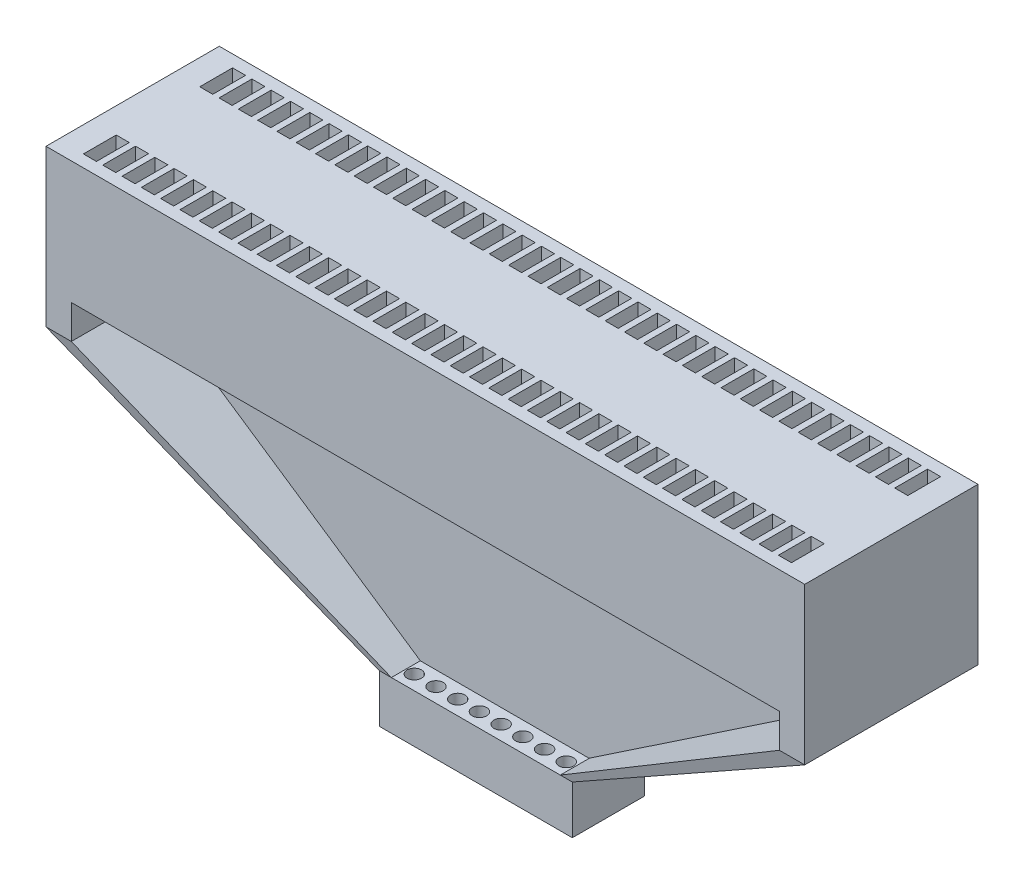
SolidWorks part; units mm, degrees
ref_plane "Front Plane" through (0, 0, 0) normal (0, 0, 1) x (1, 0, 0)
ref_plane "Top Plane" through (0, 0, 0) normal (0, 1, 0) x (1, 0, 0)
ref_plane "Right Plane" through (0, 0, 0) normal (1, 0, 0) x (0, 0, -1)
sketch "main block" plane through (0, 0, 0) normal (0, 1, 0) x (1, 0, 0)
  line L1 (7.86, -1.795) -> (-7.86, -1.795)
  line L2 (7.86, -1.795) -> (7.86, 1.795)
  line L3 (7.86, 1.795) -> (-7.86, 1.795)
  line L4 (-7.86, -1.795) -> (-7.86, 1.795)
  line L5 (7.86, -1.795) -> (-7.86, 1.795) construction
  line L6 (7.86, 1.795) -> (-7.86, -1.795) construction
  point P0 (0, 0)
  dimension "D1" = 15.72
  dimension "D2" = 3.59
extrude "Main Well Block" add sketch "main block" against normal blind 2.54
sketch "well sketch" plane through (0, 0, 0) normal (0, 1, 0) x (1, 0, 0)
  line L0 (7.86, -1.795) -> (7.86, 1.795) construction
  line L1 (7.3349, 1.545) -> (7.0649, 1.545)
  line L2 (7.3349, 1.545) -> (7.3349, 0.865)
  line L3 (7.3349, 0.865) -> (7.0649, 0.865)
  line L4 (7.0649, 1.545) -> (7.0649, 0.865)
  line L5 (7.86, 1.795) -> (-7.86, 1.795) construction
  line L6 (6.9349, 1.545) -> (6.6649, 1.545)
  line L7 (6.9349, 1.545) -> (6.9349, 0.865)
  line L8 (6.9349, 0.865) -> (6.6649, 0.865)
  line L9 (6.6649, 1.545) -> (6.6649, 0.865)
  line L10 (6.5349, 1.545) -> (6.2649, 1.545)
  line L11 (6.5349, 1.545) -> (6.5349, 0.865)
  line L12 (6.5349, 0.865) -> (6.2649, 0.865)
  line L13 (6.2649, 1.545) -> (6.2649, 0.865)
  line L14 (6.1349, 1.545) -> (5.8649, 1.545)
  line L15 (6.1349, 1.545) -> (6.1349, 0.865)
  line L16 (6.1349, 0.865) -> (5.8649, 0.865)
  line L17 (5.8649, 1.545) -> (5.8649, 0.865)
  line L18 (5.7349, 1.545) -> (5.4649, 1.545)
  line L19 (5.7349, 1.545) -> (5.7349, 0.865)
  line L20 (5.7349, 0.865) -> (5.4649, 0.865)
  line L21 (5.4649, 1.545) -> (5.4649, 0.865)
  line L22 (5.3349, 1.545) -> (5.0649, 1.545)
  line L23 (5.3349, 1.545) -> (5.3349, 0.865)
  line L24 (5.3349, 0.865) -> (5.0649, 0.865)
  line L25 (5.0649, 1.545) -> (5.0649, 0.865)
  line L26 (4.9349, 1.545) -> (4.6649, 1.545)
  line L27 (4.9349, 1.545) -> (4.9349, 0.865)
  line L28 (4.9349, 0.865) -> (4.6649, 0.865)
  line L29 (4.6649, 1.545) -> (4.6649, 0.865)
  line L30 (4.5349, 1.545) -> (4.2649, 1.545)
  line L31 (4.5349, 1.545) -> (4.5349, 0.865)
  line L32 (4.5349, 0.865) -> (4.2649, 0.865)
  line L33 (4.2649, 1.545) -> (4.2649, 0.865)
  line L34 (4.135, 1.545) -> (3.865, 1.545)
  line L35 (4.135, 1.545) -> (4.135, 0.865)
  line L36 (4.135, 0.865) -> (3.865, 0.865)
  line L37 (3.865, 1.545) -> (3.865, 0.865)
  line L38 (3.735, 1.545) -> (3.465, 1.545)
  line L39 (3.735, 1.545) -> (3.735, 0.865)
  line L40 (3.735, 0.865) -> (3.465, 0.865)
  line L41 (3.465, 1.545) -> (3.465, 0.865)
  line L42 (3.335, 1.545) -> (3.065, 1.545)
  line L43 (3.335, 1.545) -> (3.335, 0.865)
  line L44 (3.335, 0.865) -> (3.065, 0.865)
  line L45 (3.065, 1.545) -> (3.065, 0.865)
  line L46 (2.935, 1.545) -> (2.665, 1.545)
  line L47 (2.935, 1.545) -> (2.935, 0.865)
  line L48 (2.935, 0.865) -> (2.665, 0.865)
  line L49 (2.665, 1.545) -> (2.665, 0.865)
  line L50 (2.535, 1.545) -> (2.265, 1.545)
  line L51 (2.535, 1.545) -> (2.535, 0.865)
  line L52 (2.535, 0.865) -> (2.265, 0.865)
  line L53 (2.265, 1.545) -> (2.265, 0.865)
  line L54 (2.135, 1.545) -> (1.865, 1.545)
  line L55 (2.135, 1.545) -> (2.135, 0.865)
  line L56 (2.135, 0.865) -> (1.865, 0.865)
  line L57 (1.865, 1.545) -> (1.865, 0.865)
  line L58 (1.735, 1.545) -> (1.465, 1.545)
  line L59 (1.735, 1.545) -> (1.735, 0.865)
  line L60 (1.735, 0.865) -> (1.465, 0.865)
  line L61 (1.465, 1.545) -> (1.465, 0.865)
  line L62 (1.335, 1.545) -> (1.065, 1.545)
  line L63 (1.335, 1.545) -> (1.335, 0.865)
  line L64 (1.335, 0.865) -> (1.065, 0.865)
  line L65 (1.065, 1.545) -> (1.065, 0.865)
  line L66 (0.935, 1.545) -> (0.665, 1.545)
  line L67 (0.935, 1.545) -> (0.935, 0.865)
  line L68 (0.935, 0.865) -> (0.665, 0.865)
  line L69 (0.665, 1.545) -> (0.665, 0.865)
  line L70 (0.535, 1.545) -> (0.265, 1.545)
  line L71 (0.535, 1.545) -> (0.535, 0.865)
  line L72 (0.535, 0.865) -> (0.265, 0.865)
  line L73 (0.265, 1.545) -> (0.265, 0.865)
  line L74 (0.135, 1.545) -> (-0.135, 1.545)
  line L75 (0.135, 1.545) -> (0.135, 0.865)
  line L76 (0.135, 0.865) -> (-0.135, 0.865)
  line L77 (-0.135, 1.545) -> (-0.135, 0.865)
  line L78 (-0.265, 1.545) -> (-0.535, 1.545)
  line L79 (-0.265, 1.545) -> (-0.265, 0.865)
  line L80 (-0.265, 0.865) -> (-0.535, 0.865)
  line L81 (-0.535, 1.545) -> (-0.535, 0.865)
  line L82 (-0.665, 1.545) -> (-0.935, 1.545)
  line L83 (-0.665, 1.545) -> (-0.665, 0.865)
  line L84 (-0.665, 0.865) -> (-0.935, 0.865)
  line L85 (-0.935, 1.545) -> (-0.935, 0.865)
  line L86 (-1.065, 1.545) -> (-1.335, 1.545)
  line L87 (-1.065, 1.545) -> (-1.065, 0.865)
  line L88 (-1.065, 0.865) -> (-1.335, 0.865)
  line L89 (-1.335, 1.545) -> (-1.335, 0.865)
  line L90 (-1.465, 1.545) -> (-1.735, 1.545)
  line L91 (-1.465, 1.545) -> (-1.465, 0.865)
  line L92 (-1.465, 0.865) -> (-1.735, 0.865)
  line L93 (-1.735, 1.545) -> (-1.735, 0.865)
  line L94 (-1.8649, 1.545) -> (-2.1349, 1.545)
  line L95 (-1.8649, 1.545) -> (-1.8649, 0.865)
  line L96 (-1.8649, 0.865) -> (-2.1349, 0.865)
  line L97 (-2.1349, 1.545) -> (-2.1349, 0.865)
  line L98 (-2.2649, 1.545) -> (-2.5349, 1.545)
  line L99 (-2.2649, 1.545) -> (-2.2649, 0.865)
  line L100 (-2.2649, 0.865) -> (-2.5349, 0.865)
  line L101 (-2.5349, 1.545) -> (-2.5349, 0.865)
  line L102 (-2.6649, 1.545) -> (-2.9349, 1.545)
  line L103 (-2.6649, 1.545) -> (-2.6649, 0.865)
  line L104 (-2.6649, 0.865) -> (-2.9349, 0.865)
  line L105 (-2.9349, 1.545) -> (-2.9349, 0.865)
  line L106 (-3.0649, 1.545) -> (-3.3349, 1.545)
  line L107 (-3.0649, 1.545) -> (-3.0649, 0.865)
  line L108 (-3.0649, 0.865) -> (-3.3349, 0.865)
  line L109 (-3.3349, 1.545) -> (-3.3349, 0.865)
  line L110 (-3.4649, 1.545) -> (-3.7349, 1.545)
  line L111 (-3.4649, 1.545) -> (-3.4649, 0.865)
  line L112 (-3.4649, 0.865) -> (-3.7349, 0.865)
  line L113 (-3.7349, 1.545) -> (-3.7349, 0.865)
  line L114 (-3.8649, 1.545) -> (-4.1349, 1.545)
  line L115 (-3.8649, 1.545) -> (-3.8649, 0.865)
  line L116 (-3.8649, 0.865) -> (-4.1349, 0.865)
  line L117 (-4.1349, 1.545) -> (-4.1349, 0.865)
  line L118 (-4.2649, 1.545) -> (-4.5349, 1.545)
  line L119 (-4.2649, 1.545) -> (-4.2649, 0.865)
  line L120 (-4.2649, 0.865) -> (-4.5349, 0.865)
  line L121 (-4.5349, 1.545) -> (-4.5349, 0.865)
  line L122 (-4.6649, 1.545) -> (-4.9349, 1.545)
  line L123 (-4.6649, 1.545) -> (-4.6649, 0.865)
  line L124 (-4.6649, 0.865) -> (-4.9349, 0.865)
  line L125 (-4.9349, 1.545) -> (-4.9349, 0.865)
  line L126 (-5.0649, 1.545) -> (-5.3349, 1.545)
  line L127 (-5.0649, 1.545) -> (-5.0649, 0.865)
  line L128 (-5.0649, 0.865) -> (-5.3349, 0.865)
  line L129 (-5.3349, 1.545) -> (-5.3349, 0.865)
  line L130 (-5.4649, 1.545) -> (-5.7349, 1.545)
  line L131 (-5.4649, 1.545) -> (-5.4649, 0.865)
  line L132 (-5.4649, 0.865) -> (-5.7349, 0.865)
  line L133 (-5.7349, 1.545) -> (-5.7349, 0.865)
  line L134 (-5.8649, 1.545) -> (-6.1349, 1.545)
  line L135 (-5.8649, 1.545) -> (-5.8649, 0.865)
  line L136 (-5.8649, 0.865) -> (-6.1349, 0.865)
  line L137 (-6.1349, 1.545) -> (-6.1349, 0.865)
  line L138 (-6.2649, 1.545) -> (-6.5349, 1.545)
  line L139 (-6.2649, 1.545) -> (-6.2649, 0.865)
  line L140 (-6.2649, 0.865) -> (-6.5349, 0.865)
  line L141 (-6.5349, 1.545) -> (-6.5349, 0.865)
  line L142 (6.9349, -0.865) -> (6.6649, -0.865)
  line L143 (6.9349, -0.865) -> (6.9349, -1.545)
  line L144 (6.9349, -1.545) -> (6.6649, -1.545)
  line L145 (6.6649, -0.865) -> (6.6649, -1.545)
  line L146 (6.5349, -0.865) -> (6.2649, -0.865)
  line L147 (6.5349, -0.865) -> (6.5349, -1.545)
  line L148 (6.5349, -1.545) -> (6.2649, -1.545)
  line L149 (6.2649, -0.865) -> (6.2649, -1.545)
  line L150 (6.1349, -0.865) -> (5.8649, -0.865)
  line L151 (6.1349, -0.865) -> (6.1349, -1.545)
  line L152 (6.1349, -1.545) -> (5.8649, -1.545)
  line L153 (5.8649, -0.865) -> (5.8649, -1.545)
  line L154 (5.7349, -0.865) -> (5.4649, -0.865)
  line L155 (5.7349, -0.865) -> (5.7349, -1.545)
  line L156 (5.7349, -1.545) -> (5.4649, -1.545)
  line L157 (5.4649, -0.865) -> (5.4649, -1.545)
  line L158 (5.3349, -0.865) -> (5.0649, -0.865)
  line L159 (5.3349, -0.865) -> (5.3349, -1.545)
  line L160 (5.3349, -1.545) -> (5.0649, -1.545)
  line L161 (5.0649, -0.865) -> (5.0649, -1.545)
  line L162 (4.9349, -0.865) -> (4.6649, -0.865)
  line L163 (4.9349, -0.865) -> (4.9349, -1.545)
  line L164 (4.9349, -1.545) -> (4.6649, -1.545)
  line L165 (4.6649, -0.865) -> (4.6649, -1.545)
  line L166 (4.5349, -0.865) -> (4.2649, -0.865)
  line L167 (4.5349, -0.865) -> (4.5349, -1.545)
  line L168 (4.5349, -1.545) -> (4.2649, -1.545)
  line L169 (4.2649, -0.865) -> (4.2649, -1.545)
  line L170 (4.135, -0.865) -> (3.865, -0.865)
  line L171 (4.135, -0.865) -> (4.135, -1.545)
  line L172 (4.135, -1.545) -> (3.865, -1.545)
  line L173 (3.865, -0.865) -> (3.865, -1.545)
  line L174 (3.735, -0.865) -> (3.465, -0.865)
  line L175 (3.735, -0.865) -> (3.735, -1.545)
  line L176 (3.735, -1.545) -> (3.465, -1.545)
  line L177 (3.465, -0.865) -> (3.465, -1.545)
  line L178 (3.335, -0.865) -> (3.065, -0.865)
  line L179 (3.335, -0.865) -> (3.335, -1.545)
  line L180 (3.335, -1.545) -> (3.065, -1.545)
  line L181 (3.065, -0.865) -> (3.065, -1.545)
  line L182 (2.935, -0.865) -> (2.665, -0.865)
  line L183 (2.935, -0.865) -> (2.935, -1.545)
  line L184 (2.935, -1.545) -> (2.665, -1.545)
  line L185 (2.665, -0.865) -> (2.665, -1.545)
  line L186 (2.535, -0.865) -> (2.265, -0.865)
  line L187 (2.535, -0.865) -> (2.535, -1.545)
  line L188 (2.535, -1.545) -> (2.265, -1.545)
  line L189 (2.265, -0.865) -> (2.265, -1.545)
  line L190 (2.135, -0.865) -> (1.865, -0.865)
  line L191 (2.135, -0.865) -> (2.135, -1.545)
  line L192 (2.135, -1.545) -> (1.865, -1.545)
  line L193 (1.865, -0.865) -> (1.865, -1.545)
  line L194 (1.735, -0.865) -> (1.465, -0.865)
  line L195 (1.735, -0.865) -> (1.735, -1.545)
  line L196 (1.735, -1.545) -> (1.465, -1.545)
  line L197 (1.465, -0.865) -> (1.465, -1.545)
  line L198 (1.335, -0.865) -> (1.065, -0.865)
  line L199 (1.335, -0.865) -> (1.335, -1.545)
  line L200 (1.335, -1.545) -> (1.065, -1.545)
  line L201 (1.065, -0.865) -> (1.065, -1.545)
  line L202 (0.935, -0.865) -> (0.665, -0.865)
  line L203 (0.935, -0.865) -> (0.935, -1.545)
  line L204 (0.935, -1.545) -> (0.665, -1.545)
  line L205 (0.665, -0.865) -> (0.665, -1.545)
  line L206 (0.535, -0.865) -> (0.265, -0.865)
  line L207 (0.535, -0.865) -> (0.535, -1.545)
  line L208 (0.535, -1.545) -> (0.265, -1.545)
  line L209 (0.265, -0.865) -> (0.265, -1.545)
  line L210 (0.135, -0.865) -> (-0.135, -0.865)
  line L211 (0.135, -0.865) -> (0.135, -1.545)
  line L212 (0.135, -1.545) -> (-0.135, -1.545)
  line L213 (-0.135, -0.865) -> (-0.135, -1.545)
  line L214 (-0.265, -0.865) -> (-0.535, -0.865)
  line L215 (-0.265, -0.865) -> (-0.265, -1.545)
  line L216 (-0.265, -1.545) -> (-0.535, -1.545)
  line L217 (-0.535, -0.865) -> (-0.535, -1.545)
  line L218 (-0.665, -0.865) -> (-0.935, -0.865)
  line L219 (-0.665, -0.865) -> (-0.665, -1.545)
  line L220 (-0.665, -1.545) -> (-0.935, -1.545)
  line L221 (-0.935, -0.865) -> (-0.935, -1.545)
  line L222 (-1.065, -0.865) -> (-1.335, -0.865)
  line L223 (-1.065, -0.865) -> (-1.065, -1.545)
  line L224 (-1.065, -1.545) -> (-1.335, -1.545)
  line L225 (-1.335, -0.865) -> (-1.335, -1.545)
  line L226 (-1.465, -0.865) -> (-1.735, -0.865)
  line L227 (-1.465, -0.865) -> (-1.465, -1.545)
  line L228 (-1.465, -1.545) -> (-1.735, -1.545)
  line L229 (-1.735, -0.865) -> (-1.735, -1.545)
  line L230 (-1.8649, -0.865) -> (-2.1349, -0.865)
  line L231 (-1.8649, -0.865) -> (-1.8649, -1.545)
  line L232 (-1.8649, -1.545) -> (-2.1349, -1.545)
  line L233 (-2.1349, -0.865) -> (-2.1349, -1.545)
  line L234 (-2.2649, -0.865) -> (-2.5349, -0.865)
  line L235 (-2.2649, -0.865) -> (-2.2649, -1.545)
  line L236 (-2.2649, -1.545) -> (-2.5349, -1.545)
  line L237 (-2.5349, -0.865) -> (-2.5349, -1.545)
  line L238 (-2.6649, -0.865) -> (-2.9349, -0.865)
  line L239 (-2.6649, -0.865) -> (-2.6649, -1.545)
  line L240 (-2.6649, -1.545) -> (-2.9349, -1.545)
  line L241 (-2.9349, -0.865) -> (-2.9349, -1.545)
  line L242 (-3.0649, -0.865) -> (-3.3349, -0.865)
  line L243 (-3.0649, -0.865) -> (-3.0649, -1.545)
  line L244 (-3.0649, -1.545) -> (-3.3349, -1.545)
  line L245 (-3.3349, -0.865) -> (-3.3349, -1.545)
  line L246 (-3.4649, -0.865) -> (-3.7349, -0.865)
  line L247 (-3.4649, -0.865) -> (-3.4649, -1.545)
  line L248 (-3.4649, -1.545) -> (-3.7349, -1.545)
  line L249 (-3.7349, -0.865) -> (-3.7349, -1.545)
  line L250 (-3.8649, -0.865) -> (-4.1349, -0.865)
  line L251 (-3.8649, -0.865) -> (-3.8649, -1.545)
  line L252 (-3.8649, -1.545) -> (-4.1349, -1.545)
  line L253 (-4.1349, -0.865) -> (-4.1349, -1.545)
  line L254 (-4.2649, -0.865) -> (-4.5349, -0.865)
  line L255 (-4.2649, -0.865) -> (-4.2649, -1.545)
  line L256 (-4.2649, -1.545) -> (-4.5349, -1.545)
  line L257 (-4.5349, -0.865) -> (-4.5349, -1.545)
  line L258 (-4.6649, -0.865) -> (-4.9349, -0.865)
  line L259 (-4.6649, -0.865) -> (-4.6649, -1.545)
  line L260 (-4.6649, -1.545) -> (-4.9349, -1.545)
  line L261 (-4.9349, -0.865) -> (-4.9349, -1.545)
  line L262 (-5.0649, -0.865) -> (-5.3349, -0.865)
  line L263 (-5.0649, -0.865) -> (-5.0649, -1.545)
  line L264 (-5.0649, -1.545) -> (-5.3349, -1.545)
  line L265 (-5.3349, -0.865) -> (-5.3349, -1.545)
  line L266 (-5.4649, -0.865) -> (-5.7349, -0.865)
  line L267 (-5.4649, -0.865) -> (-5.4649, -1.545)
  line L268 (-5.4649, -1.545) -> (-5.7349, -1.545)
  line L269 (-5.7349, -0.865) -> (-5.7349, -1.545)
  line L270 (-5.8649, -0.865) -> (-6.1349, -0.865)
  line L271 (-5.8649, -0.865) -> (-5.8649, -1.545)
  line L272 (-5.8649, -1.545) -> (-6.1349, -1.545)
  line L273 (-6.1349, -0.865) -> (-6.1349, -1.545)
  line L274 (-6.2649, -0.865) -> (-6.5349, -0.865)
  line L275 (-6.2649, -0.865) -> (-6.2649, -1.545)
  line L276 (-6.2649, -1.545) -> (-6.5349, -1.545)
  line L277 (-6.5349, -0.865) -> (-6.5349, -1.545)
  line L278 (7.3349, -0.865) -> (7.0649, -0.865)
  line L279 (7.3349, -0.865) -> (7.3349, -1.545)
  line L280 (7.3349, -1.545) -> (7.0649, -1.545)
  line L281 (7.0649, -0.865) -> (7.0649, -1.545)
  line L282 (-6.6649, 1.545) -> (-6.9349, 1.545)
  line L283 (-6.6649, 1.545) -> (-6.6649, 0.865)
  line L284 (-6.6649, 0.865) -> (-6.9349, 0.865)
  line L285 (-6.9349, 1.545) -> (-6.9349, 0.865)
  line L286 (-7.0649, 1.545) -> (-7.3349, 1.545)
  line L287 (-7.0649, 1.545) -> (-7.0649, 0.865)
  line L288 (-7.0649, 0.865) -> (-7.3349, 0.865)
  line L289 (-7.3349, 1.545) -> (-7.3349, 0.865)
  line L290 (-6.6649, -0.865) -> (-6.9349, -0.865)
  line L291 (-6.6649, -0.865) -> (-6.6649, -1.545)
  line L292 (-6.6649, -1.545) -> (-6.9349, -1.545)
  line L293 (-6.9349, -0.865) -> (-6.9349, -1.545)
  line L294 (-7.0649, -0.865) -> (-7.3349, -0.865)
  line L295 (-7.0649, -0.865) -> (-7.0649, -1.545)
  line L296 (-7.0649, -1.545) -> (-7.3349, -1.545)
  line L297 (-7.3349, -0.865) -> (-7.3349, -1.545)
  line L301 (-7.86, -1.795) -> (7.86, -1.795) construction
  dimension "D1" = 0.27
  dimension "D2" = 0.68
  dimension "D3" = 0.5251
  dimension "D4" = 0.25
  dimension "D5" = 37
  dimension "D6" = 2
extrude "wells" cut sketch "well sketch" against normal blind 2.54
sketch "support beams" plane through (0, -2.54, 0) normal (0, -1, 0) x (1, 0, 0)
  line L0 (-7.86, 1.795) -> (7.86, 1.795) construction
  line L1 (-7.86, -1.795) -> (-7.3349, -1.795)
  line L2 (-7.86, -1.795) -> (-7.86, 1.795)
  line L3 (-7.86, 1.795) -> (-7.3349, 1.795)
  line L4 (-7.3349, -1.795) -> (-7.3349, 1.795)
  line L6 (7.86, -1.795) -> (7.3349, -1.795)
  line L7 (7.86, -1.795) -> (7.86, 1.795)
  line L8 (7.86, 1.795) -> (7.3349, 1.795)
  line L9 (7.3349, -1.795) -> (7.3349, 1.795)
extrude "support beams extr" add sketch "support beams" along normal blind 0.7
sketch "wall divider sketch" plane through (0, -2.54, 0) normal (0, -1, 0) x (-1, 0, 0)
  line L0 (7.3349, 1.795) -> (7.3349, -1.795) construction
  line L1 (-7.3349, 0.15) -> (7.3349, 0.15)
  line L2 (-7.3349, 0.15) -> (-7.3349, -0.15)
  line L3 (-7.3349, -0.15) -> (7.3349, -0.15)
  line L4 (7.3349, 0.15) -> (7.3349, -0.15)
  line L5 (-7.3349, 0.15) -> (7.3349, -0.15) construction
  line L6 (-7.3349, -0.15) -> (7.3349, 0.15) construction
  point P0 (0, 0)
  dimension "D1" = 0.3
ref_plane "Plane1" through (0, -7, 0) normal (0, 1, 0) x (1, 0, 0)
sketch "exit base sketch" plane through (0, -7, 0) normal (0, 1, 0) x (1, 0, 0)
  line L1 (2, 0.75) -> (-2, 0.75)
  line L2 (2, 0.75) -> (2, -0.75)
  line L3 (2, -0.75) -> (-2, -0.75)
  line L4 (-2, 0.75) -> (-2, -0.75)
  line L5 (2, 0.75) -> (-2, -0.75) construction
  line L6 (2, -0.75) -> (-2, 0.75) construction
  circle A0 centre (1.575, -0.45) radius 0.15
  circle A1 centre (1.125, -0.45) radius 0.15
  circle A2 centre (0.675, -0.45) radius 0.15
  circle A3 centre (0.225, -0.45) radius 0.15
  circle A4 centre (-0.225, -0.45) radius 0.15
  circle A5 centre (-0.675, -0.45) radius 0.15
  circle A6 centre (-1.125, -0.45) radius 0.15
  circle A7 centre (-1.575, -0.45) radius 0.15
  circle A8 centre (1.125, 0.45) radius 0.15
  circle A9 centre (0.675, 0.45) radius 0.15
  circle A10 centre (0.225, 0.45) radius 0.15
  circle A11 centre (-0.225, 0.45) radius 0.15
  circle A12 centre (-0.675, 0.45) radius 0.15
  circle A13 centre (-1.125, 0.45) radius 0.15
  circle A14 centre (-1.575, 0.45) radius 0.15
  circle A15 centre (1.575, 0.45) radius 0.15
  point P0 (0, 0)
  dimension "D3" = 8
  dimension "D1" = 4
  dimension "D2" = 1.5
  dimension "D5" = 0.425
  dimension "D6" = 0.3
  dimension "D4" = 2
sketch "Sketch6" plane through (0, -7, 0) normal (0, 1, 0) x (1, 0, 0)
  line L0 (2, -0.75) -> (-2, -0.75) construction
  line L1 (-2, 0.75) -> (-1.75, 0.75)
  line L2 (-2, 0.75) -> (-2, -0.75)
  line L3 (-2, -0.75) -> (-1.75, -0.75)
  line L4 (-1.75, 0.75) -> (-1.75, -0.75)
  dimension "D1" = 0.25
loft "arm1" add profiles "Sketch6" section "Sketch6" section face at (-7.5974, -3.24, 0)
sketch "Sketch7" plane through (0, -7, 0) normal (0, 1, 0) x (1, 0, 0)
  line L0 (2, -0.75) -> (-2, -0.75) construction
  line L1 (2, 0.75) -> (1.75, 0.75)
  line L2 (2, 0.75) -> (2, -0.75)
  line L3 (2, -0.75) -> (1.75, -0.75)
  line L4 (1.75, 0.75) -> (1.75, -0.75)
  dimension "D1" = 0.25
loft "arm2" add profiles "Sketch7" section "Sketch7" section face at (7.5975, -3.24, 0)
sketch "Sketch8" plane through (0, -7, 0) normal (0, 1, 0) x (1, 0, 0)
  line L0 (7.3349, -0.15) -> (-7.3349, -0.15) construction
  line L1 (1.7469, 0.15) -> (-1.7469, 0.15)
  line L2 (1.7469, 0.15) -> (1.7469, -0.15)
  line L3 (1.7469, -0.15) -> (-1.7469, -0.15)
  line L4 (-1.7469, 0.15) -> (-1.7469, -0.15)
  line L5 (1.7469, 0.15) -> (-1.7469, -0.15) construction
  line L6 (1.7469, -0.15) -> (-1.7469, 0.15) construction
  point P0 (0, 0)
extrude "Boss-Extrude3" add sketch "wall divider sketch" along normal blind 0.7
loft "divider wall" add profiles "Sketch8" section face at (0, -3.24, 0) section "Sketch8"
ref_plane "Plane2" through (0, -7.3, 0) normal (0, 1, 0) x (1, 0, 0)
extrude "Boss-Extrude4" add sketch "exit base sketch" against normal blind 1 separate body
